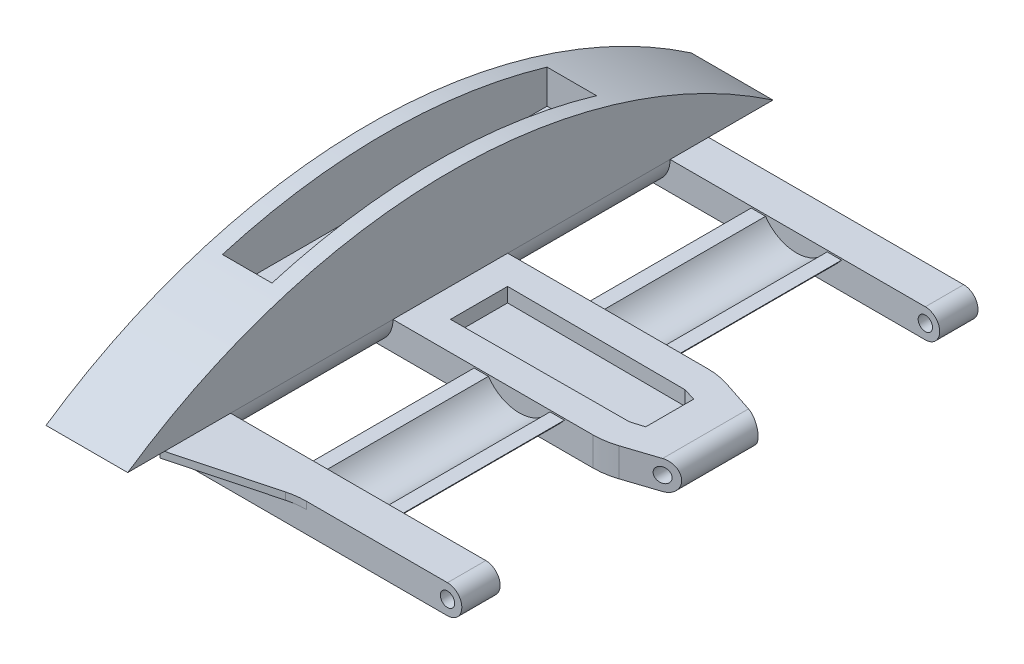
SolidWorks part; units mm, degrees
ref_plane "Front Plane" through (0, 0, 0) normal (0, 0, 1) x (1, 0, 0)
ref_plane "Top Plane" through (0, 0, 0) normal (0, 1, 0) x (1, 0, 0)
ref_plane "Right Plane" through (0, 0, 0) normal (1, 0, 0) x (0, 0, -1)
sketch "Sketch2" plane through (0, 0, 0) normal (0, 1, 0) x (1, 0, 0)
  line L4 (0, 45) -> (0, 0)
  line L5 (0, 0) -> (10, 0)
  line L6 (10, 0) -> (10, 45)
  line L7 (10, 45) -> (0, 45)
  line L8 (0, 40.5) -> (10, 40.5) construction
  line L9 (0, 4.5) -> (10, 4.5) construction
  dimension "D1" = 45
  dimension "D2" = 4.5
  dimension "D3" = 4.5
  dimension "D4" = 10
sketch "Sketch3" plane through (0, 0, 0) normal (1, 0, 0) x (0, 0, -1)
  line L0 (0, 0) -> (45, 0)
  arc A0 (0, 0) -> (45, 0) centre (22.5, -33.0719) cw
  dimension "D1" = 40
extrude "Boss-Extrude1" add sketch "Sketch3" along normal blind 2.7
sketch "Sketch4" plane through (0, 0, 0) normal (0, -1, 0) x (1, 0, 0)
  line L0 (0, -45) -> (0, 0) construction
  line L1 (2.7, 0) -> (2.7, -45) construction
  line L2 (2.7, -22.5) -> (30.4189, -22.5) construction
  line L3 (2.7, -44.1622) -> (2.7, -45)
  line L4 (2.7, -45) -> (0, -45)
  line L5 (0, -45) -> (0, -44.1622)
  line L6 (2.7, 0) -> (0, 0)
  line L7 (2.7, -0.8378) -> (2.7, 0)
  line L8 (0, 0) -> (0, -0.8378)
  arc A0 (0, -44.1622) -> (2.7, -44.1622) centre (1.35, -43.4934) ccw
  arc A1 (0, -0.8378) -> (2.7, -0.8378) centre (1.35, -1.5066) cw
  point P3 (1.35, -45)
  dimension "D1" = 1.5066
sketch "Sketch6" plane through (0, 0, 0) normal (0, -1, 0) x (1, 0, 0)
  line L1 (0, -4.5) -> (21.5, -4.5)
  line L2 (0, -4.5) -> (0, -40.5)
  line L3 (0, -40.5) -> (21.5, -40.5)
  line L4 (21.5, -4.5) -> (21.5, -40.5)
  line L6 (0, -4.5) -> (10, -4.5) construction
  line L7 (0, -40.5) -> (10, -40.5) construction
  line L8 (0, -45) -> (0, 0) construction
  dimension "D1" = 21.5
extrude "Boss-Extrude2" add sketch "Sketch6" along normal blind 2
sketch "Sketch7" plane through (0, 0, 0) normal (0, 1, 0) x (1, 0, 0)
  line L0 (21.5, 22.5) -> (-9.3767, 22.5) construction
  line L1 (21.5, 40.5) -> (21.5, 4.5) construction
  line L2 (2.7, 0) -> (2.7, 45) construction
  line L3 (2.7, 26.5) -> (21.5, 26.5)
  line L4 (2.7, 26.5) -> (2.7, 37.827)
  line L5 (2.7, 37.827) -> (21.5, 37.827)
  line L6 (21.5, 26.5) -> (21.5, 37.827)
  line L7 (2.7, 32.1635) -> (21.5, 32.1635) construction
  line L9 (2.7, 7.173) -> (21.5, 7.173)
  line L10 (21.5, 18.5) -> (21.5, 7.173)
  line L11 (2.7, 18.5) -> (21.5, 18.5)
  line L12 (2.7, 18.5) -> (2.7, 7.173)
  line L13 (2.7, 40.5) -> (21.5, 40.5) construction
  dimension "D1" = 2.673
  dimension "D2" = 8
extrude "Cut-Extrude3" cut sketch "Sketch7" against normal blind 2 contours L11 L9 | L5 L9 L3 L11
sketch "Sketch8" plane through (0, 0, -40.5) normal (0, 0, -1) x (-1, 0, 0)
  line L0 (-21.5, -2) -> (-21.5, 0) construction
  line L1 (-2.7, 0) -> (-21.5, 0) construction
  line L2 (0, -2) -> (-21.5, -2) construction
  line L3 (-20.5, 0) -> (-21.5, 0)
  line L4 (-21.5, 0) -> (-21.5, -2)
  line L5 (-21.5, -2) -> (-20.5, -2)
  circle A0 centre (-20.5, -1) radius 1
  line M3 (-2.7, 0) -> (-21.5, 0)
  line M4 (-21.5, 0) -> (-21.5, -2)
  line M5 (-21.5, -2) -> (0, -2)
extrude "Cut-Extrude4" cut sketch "Sketch8" against normal through all contours A0 M3 M4 | A0 L4 M5
sketch "Sketch10" plane through (0, 0, -40.5) normal (0, 0, -1) x (-1, 0, 0)
  circle A0 centre (-20.5, -1) radius 0.5
  dimension "D1" = 1
extrude "Cut-Extrude5" cut sketch "Sketch10" against normal through all
sketch "Sketch11" plane through (0, 0, -40.5) normal (0, 0, -1) x (-1, 0, 0)
  line L0 (0, 0) -> (-10, 0) construction
  line L1 (-11.3244, 0) -> (-8.2339, 0)
  line L2 (-11.3244, 0) -> (-11.3244, -2)
  line L3 (-11.3244, -2) -> (-8.2339, -2)
  line L4 (-8.2339, 0) -> (-8.2339, -2)
  line L5 (0, -2) -> (-20.5, -2) construction
sketch "Sketch22" plane through (0, -2, 0) normal (0, -1, 0) x (1, 0, 0)
  line L0 (0, -45) -> (0, 0) construction
  line L1 (0, -26.5) -> (2.3, -26.5)
  line L2 (0, -26.5) -> (0, -18.5)
  line L3 (0, -18.5) -> (2.3, -18.5)
  line L4 (2.3, -26.5) -> (2.3, -18.5)
  line L6 (2.7, -26.5) -> (20.5, -26.5) construction
  line L7 (2.7, -18.5) -> (20.5, -18.5) construction
  line L13 (0, -40.5) -> (10, -40.5) construction
  line L14 (0, -4.5) -> (2.3, -4.5)
  line L15 (0, -4.5) -> (0, -7.173)
  line L16 (0, -7.173) -> (2.3, -7.173)
  line L17 (2.3, -4.5) -> (2.3, -7.173)
  line L18 (0, -37.827) -> (2.3, -37.827)
  line L19 (0, -37.827) -> (0, -40.5)
  line L20 (0, -40.5) -> (2.3, -40.5)
  line L21 (2.3, -37.827) -> (2.3, -40.5)
  line L22 (2.7, -37.827) -> (20.5, -37.827) construction
  line L23 (2.7, -7.173) -> (20.5, -7.173) construction
  dimension "D1" = 2.3
  dimension "D2" = 2.3
  dimension "D3" = 2.3
sketch "Sketch23" plane through (0, 0, 0) normal (0, 1, 0) x (1, 0, 0)
  line L0 (11.878, 16.6727) -> (21.5, 19.833)
  line L1 (21.5, 18.5) -> (21.5, 26.5) construction
  line L2 (21.5, 19.833) -> (21.5, 13.5123)
  line L3 (21.5, 13.5123) -> (11.878, 16.6727)
  line L4 (21.5, 22.5) -> (-3.6609, 22.5) construction
  line L5 (21.5, 25.167) -> (21.5, 31.4877)
  line L6 (11.878, 28.3273) -> (21.5, 25.167)
  line L7 (21.5, 31.4877) -> (11.878, 28.3273)
  point P7 (21.5, 16.6727)
extrude "Cut-Extrude15" cut sketch "Sketch23" against normal blind 16 contours L5 L7 L6 | L3 L0 L2
fillet "Fillet6" radius 5 2 edges at (17.4416, -1, -26.5) (17.4416, -1, -18.5)
sketch "Sketch31" plane through (0, 0, -40.5) normal (0, 0, -1) x (-1, 0, 0)
  line L3 (-14.6564, -0.1066) -> (-8.3564, -0.1066)
  arc A2 (-14.6564, -0.1066) -> (-8.3564, -0.1066) centre (-11.5064, 2.3586) ccw
  dimension "D2" = 4
  dimension "D1" = 6.3
extrude "Boss-Extrude6" add sketch "Sketch31" against normal up to surface (36 mm away) up to face at (20, -1, -4.5)
sketch "Sketch30" plane through (0, 0, 0) normal (0, 1, 0) x (1, 0, 0)
  line L0 (2.7, 26.5) -> (2.7, 18.5)
  line L1 (2.7, 18.5) -> (17.4315, 18.5628)
  line L2 (17.4315, 18.5628) -> (20, 19.3403)
  line L3 (20, 19.3403) -> (20, 25.6597)
  line L4 (20, 25.6597) -> (17.4315, 26.4372)
  line L5 (17.4315, 26.4372) -> (2.7, 26.5)
  line L6 (17.1313, 24.4385) -> (4.7, 24.4915)
  line L7 (4.7, 24.4915) -> (4.7, 20.5085)
  line L8 (4.7, 20.5085) -> (17.1313, 20.5615)
  line L9 (17.1313, 20.5615) -> (18, 20.8245)
  line L10 (18, 20.8245) -> (18, 24.1755)
  line L11 (18, 24.1755) -> (17.1313, 24.4385)
  arc A0 (16.6415, 18.5) -> (18.2017, 18.7497) centre (16.6415, 23.5) ccw construction
  arc A1 (18.2017, 26.2503) -> (16.6415, 26.5) centre (16.6415, 21.5) ccw construction
  dimension "D1" = 2
extrude "Cut-Extrude18" cut sketch "Sketch30" against normal blind 1 contours L6 L7 L8 L9 L10 L11
ref_plane "Plane1" through (0, 6.9281, 0) normal (0, 1, 0) x (1, 0, 0)
sketch "Sketch33" plane through (0, 0, -40.5) normal (0, 0, -1) x (-1, 0, 0)
  line L1 (-13.6564, -0.1066) -> (-9.3564, -0.1066)
  line L2 (-14.6564, -0.1066) -> (-8.3564, -0.1066) construction
  arc A1 (-13.6564, -0.1066) -> (-9.3564, -0.1066) centre (-11.5064, 1.3586) ccw
  arc A3 (-14.6564, -0.1066) -> (-8.3564, -0.1066) centre (-11.5064, 2.3586) ccw construction
  dimension "D1" = 1
  dimension "D2" = 1
  dimension "D3" = 1
sketch "Sketch36" plane through (0, 0, -37.827) normal (0, 0, 1) x (1, 0, 0)
  line L0 (9.3564, -0.1066) -> (13.6564, -0.1066)
  arc A0 (9.3564, -0.1066) -> (13.6564, -0.1066) centre (11.5064, 1.3586) ccw construction
  arc A1 (9.3564, -0.1066) -> (13.6564, -0.1066) centre (11.5064, 1.3586) ccw
extrude "Cut-Extrude22" cut sketch "Sketch36" along normal up to surface (11.327 mm away) up to face at (11.5064, -0.874, -26.5)
sketch "Sketch37" plane through (0, 0, -7.173) normal (0, 0, -1) x (-1, 0, 0)
  line L0 (-13.6564, -0.1066) -> (-9.3564, -0.1066)
  arc A0 (-13.6564, -0.1066) -> (-9.3564, -0.1066) centre (-11.5064, 1.3586) ccw construction
  arc A1 (-13.6564, -0.1066) -> (-9.3564, -0.1066) centre (-11.5064, 1.3586) ccw
extrude "Cut-Extrude23" cut sketch "Sketch37" along normal up to surface (11.327 mm away) up to face at (11.5064, -0.874, -18.5)
sketch "Sketch42" plane through (0, 0, 0) normal (-1, 0, 0) x (0, 0, 1)
  line L0 (-45, 0) -> (-40.5, 0)
  line L1 (-40.5, 0) -> (-40.5, -2)
  line L2 (-40.5, -2) -> (-4.5, -2)
  line L3 (-4.5, -2) -> (-4.5, 0)
  line L4 (-4.5, 0) -> (0, 0)
  arc A3 (0, 0) -> (-45, 0) centre (-22.5, -33.0719) ccw construction
  arc A4 (0, 0) -> (-45, 0) centre (-22.5, -33.0719) ccw
extrude "Boss-Extrude10" add sketch "Sketch42" along normal blind 3
sketch "Sketch43" plane through (0, -2, 0) normal (0, -1, 0) x (1, 0, 0)
  line L0 (-3, -40.5) -> (-3, -4.5) construction
  line L1 (-3, -4.5) -> (-0.7, -4.5)
  line L2 (-3, -4.5) -> (-3, -7.173)
  line L3 (-3, -7.173) -> (-0.7, -7.173)
  line L4 (-0.7, -4.5) -> (-0.7, -7.173)
  line L5 (-3, -18.5) -> (-0.7, -18.5)
  line L6 (-3, -18.5) -> (-3, -26.5)
  line L7 (-3, -26.5) -> (-0.7, -26.5)
  line L8 (-0.7, -18.5) -> (-0.7, -26.5)
  line L9 (-3, -40.5) -> (20.5, -40.5) construction
  line L10 (-3, -37.827) -> (-0.7, -37.827)
  line L11 (-3, -37.827) -> (-3, -40.5)
  line L12 (-3, -40.5) -> (-0.7, -40.5)
  line L13 (-0.7, -37.827) -> (-0.7, -40.5)
  line L14 (2.7, -37.827) -> (20.5, -37.827) construction
  line L15 (2.7, -18.5) -> (16.6415, -18.5) construction
  line L16 (2.7, -26.5) -> (16.6415, -26.5) construction
  line L17 (2.7, -7.173) -> (20.5, -7.173) construction
  dimension "D1" = 2.3
  dimension "D2" = 2.3
  dimension "D3" = 2.3
revolve "Cut-Revolve7" cut sketch "Sketch43" angle 360 about L2
sketch "Sketch45" plane through (0, 0, -7.173) normal (0, 0, 1) x (1, 0, 0)
  line L0 (-3, -2) -> (-3, 0.3) construction
  line L2 (-0.7, -2) -> (-3, -2) construction
  circle A0 centre (-2, -1) radius 0.5
  dimension "D1" = 1
  dimension "D2" = 1
  dimension "D3" = 1
extrude "Cut-Extrude26" cut sketch "Sketch45" against normal through all
ref_plane "Plane3" through (0, 6.9281, 0) normal (0, 1, 0) x (1, 0, 0)
sketch "Sketch47" plane through (0, 6.9281, 0) normal (0, 1, 0) x (1, 0, 0)
  line L0 (2.7, 0) -> (2.7, 45) construction
  line L1 (-1.877, 33.8191) -> (1.577, 33.8191)
  line L2 (-1.877, 33.8191) -> (-1.877, 11.1809)
  line L3 (-1.877, 11.1809) -> (1.577, 11.1809)
  line L4 (1.577, 33.8191) -> (1.577, 11.1809)
  line L5 (2.7, 45) -> (-3, 45) construction
  point P6 (2.7, 22.5)
  point P7 (1.577, 22.5)
  point P8 (-0.15, 45)
  point P11 (-0.15, 33.8191)
  dimension "D1" = 1.123
extrude "Cut-Extrude27" cut sketch "Sketch47" against normal blind 4
fillet "Fillet13" radius 2 2 edges at (2.7, -2, -12.8365) (2.7, -2, -32.1635)
fillet "Fillet15" radius 1 2 edges at (-3, -2, -32.1635) (-3, -2, -12.8365)
ref_plane "Plane4" through (0, 0, -22.5) normal (0, 0, 1) x (1, 0, 0)
sketch "Sketch27" plane through (0, 0, 0) normal (0, -1, 0) x (1, 0, 0)
  line L1 (2.45, -4.5) -> (10, -4.5)
  line L2 (10, -4.5) -> (2.45, -2.5)
  line L3 (2.45, -2.5) -> (2.45, -4.5)
  line L4 (2.7, 0) -> (2.7, -4.5) construction
  dimension "D1" = 0.25
  dimension "D2" = 2
extrude "Boss-Extrude5" add sketch "Sketch27" along normal blind 0.5
fillet "Fillet7" radius 5 1 edges at (10, -0.25, -4.5)
